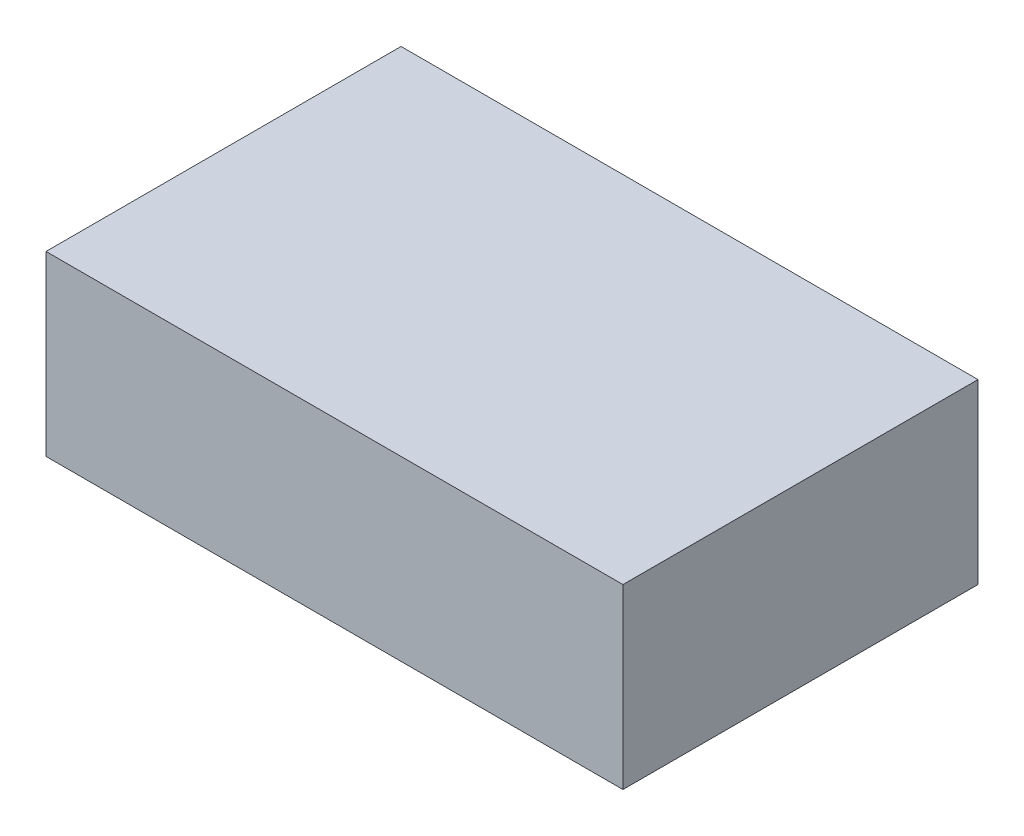
SolidWorks part; units mm, degrees
ref_plane "Front Plane" through (0, 0, 0) normal (0, 0, 1) x (1, 0, 0)
ref_plane "Top Plane" through (0, 0, 0) normal (0, 1, 0) x (1, 0, 0)
ref_plane "Right Plane" through (0, 0, 0) normal (1, 0, 0) x (0, 0, -1)
sketch "Sketch1" plane through (0, 0, 0) normal (0, 1, 0) x (1, 0, 0)
  line L1 (-65, -40) -> (65, -40)
  line L2 (-65, -40) -> (-65, 40)
  line L3 (-65, 40) -> (65, 40)
  line L4 (65, -40) -> (65, 40)
  line L5 (-65, -40) -> (65, 40) construction
  line L6 (-65, 40) -> (65, -40) construction
  point P0 (0, 0)
  dimension "D1" = 130
  dimension "D2" = 80
extrude "Boss-Extrude1" add sketch "Sketch1" along normal blind 40
ref_plane "Plane1" through (0, 20, 0) normal (0, 1, 0) x (1, 0, 0)
